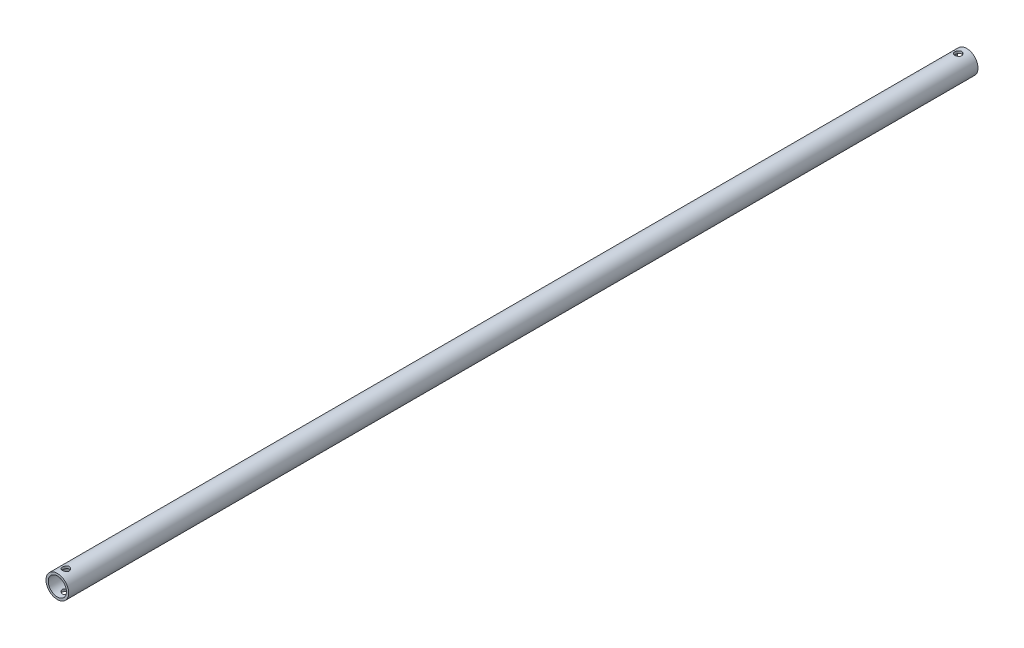
SolidWorks part; units mm, degrees
ref_plane "Płaszczyzna przednia" through (0, 0, 0) normal (0, 0, 1) x (1, 0, 0)
ref_plane "Płaszczyzna górna" through (0, 0, 0) normal (0, 1, 0) x (1, 0, 0)
ref_plane "Płaszczyzna prawa" through (0, 0, 0) normal (1, 0, 0) x (0, 0, -1)
sketch "Szkic1" plane through (0, 0, 0) normal (0, 0, 1) x (1, 0, 0)
  circle A0 centre (0, 0) radius 10
  dimension "D1" = 20
extrude "Dodanie-wyciągnięcie2" add sketch "Szkic1" along normal mid plane 800
sketch "Szkic3" plane through (0, 0, 400) normal (0, 0, 1) x (1, 0, 0)
  circle A0 centre (0, 0) radius 8
  dimension "D1" = 16
extrude "Wytnij-wyciągnięcie1" cut sketch "Szkic3" against normal through all
sketch "Szkic4" plane through (0, 0, 0) normal (0, 1, 0) x (1, 0, 0)
  line L0 (-10, -400) -> (10, -400) construction
  circle A0 centre (0, -392.5) radius 3
  dimension "D1" = 6
  dimension "D2" = 7.5
extrude "Wytnij-wyciągnięcie2" cut sketch "Szkic4" against normal through all both and the other way through all
ref_plane "Płaszczyzna1" through (0, 0, 0) normal (0, 0, -1) x (-1, 0, 0)
mirror "Lustro1" about plane through (0, 0, 0) normal (0, 0, -1) of "Wytnij-wyciągnięcie2"
